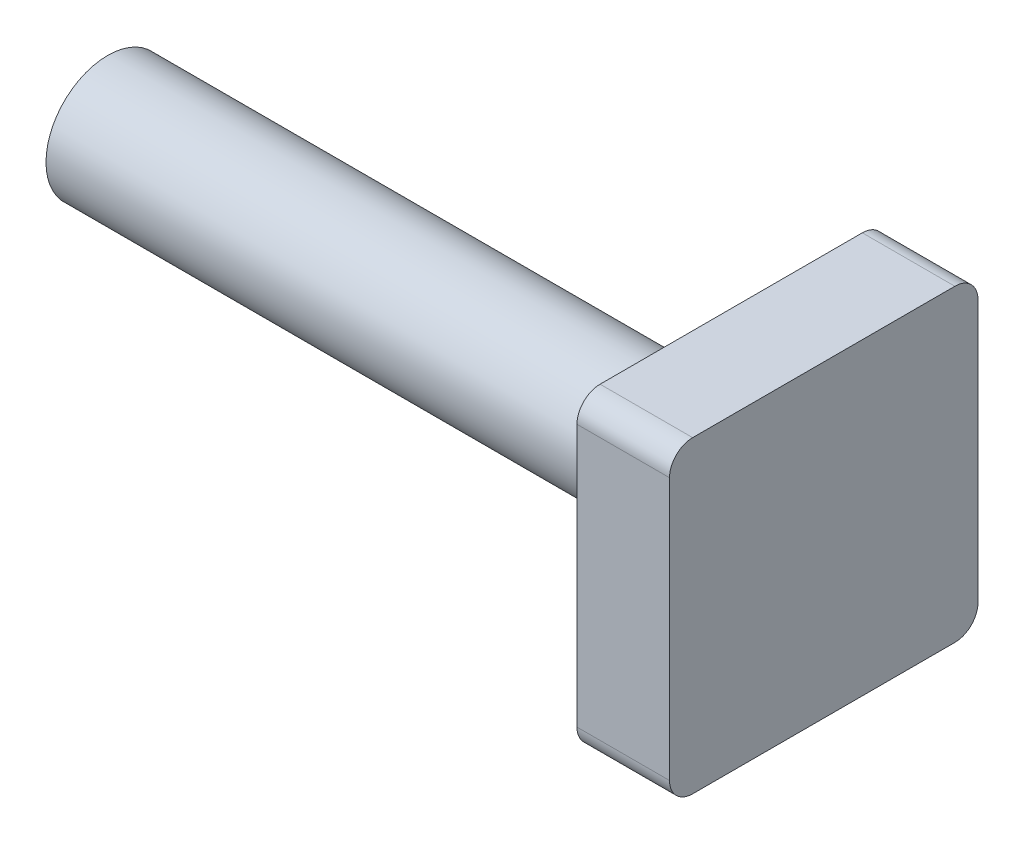
SolidWorks part; units mm, degrees
material "Ti-6Al-4VSolution treated and aged (SS)"
ref_plane "Front Plane" through (0, 0, 0) normal (0, 0, 1) x (1, 0, 0)
ref_plane "Top Plane" through (0, 0, 0) normal (0, 1, 0) x (1, 0, 0)
ref_plane "Right Plane" through (0, 0, 0) normal (1, 0, 0) x (0, 0, -1)
sketch "Sketch1" plane through (0, 0, 0) normal (1, 0, 0) x (0, 0, -1)
  line L0 (-5, 0) -> (5, 0) construction
  line L1 (-5, 5) -> (5, 5)
  line L2 (-5, 5) -> (-5, -5)
  line L3 (-5, -5) -> (5, -5)
  line L4 (5, 5) -> (5, -5)
  dimension "D1" = 10
  dimension "D2" = 10
extrude "head" add sketch "Sketch1" along normal blind 3
sketch "Sketch2" plane through (0, 0, 0) normal (-1, 0, 0) x (0, 0, 1)
  circle A0 centre (0, 0) radius 2
  dimension "D1" = 4
extrude "shaft" add sketch "Sketch2" along normal blind 20.5
cosmetic thread "Cosmetic Thread1" parameters "D1"=9.5, "D2"=3.22
fillet "head fillet" radius 0.75 4 edges at (1.5, -5, 5) (1.5, 5, 5) (1.5, 5, -5) (1.5, -5, -5)
fillet "Fillet1" radius 0.5 1 edges at (0, 0, -2)
chamfer "Chamfer1" distance 0.5 angle 30 1 edges at (-20.5, 0, 2)
